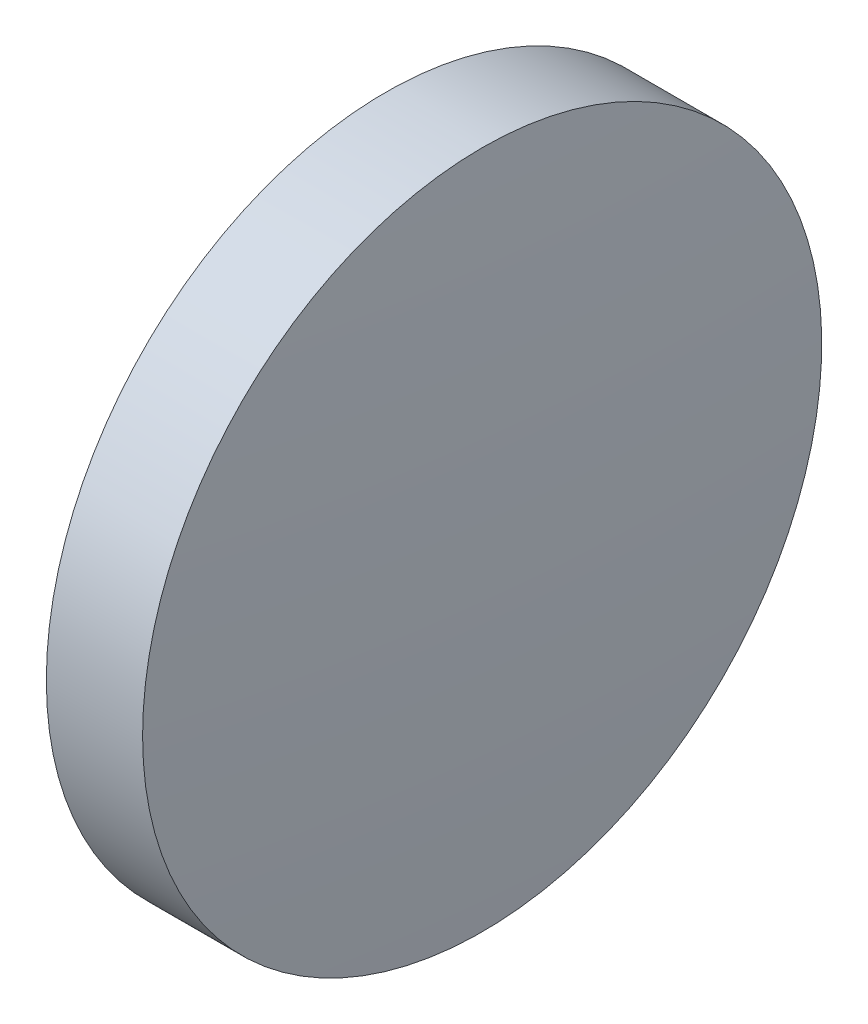
SolidWorks part; units mm, degrees
ref_plane "前视基准面" through (0, 0, 0) normal (0, 0, 1) x (1, 0, 0)
ref_plane "上视基准面" through (0, 0, 0) normal (0, 1, 0) x (1, 0, 0)
ref_plane "右视基准面" through (0, 0, 0) normal (1, 0, 0) x (0, 0, -1)
sketch "草图1" plane through (0, 0, 0) normal (0, 0, 1) x (1, 0, 0)
  line L0 (110.1654, 65.2336) -> (128.9614, 65.2336) construction
  line L1 (115.7646, 65.2336) -> (115.7646, 77.9336)
  line L2 (119.7646, 65.2336) -> (115.7646, 65.2336)
  line L5 (115.7646, 77.9336) -> (119.3646, 77.9336)
  arc A0 (119.7646, 65.2336) -> (119.3646, 77.9336) centre (-82.0479, 65.2336) ccw
revolve "旋转1" add sketch "草图1" angle 360 about L0
